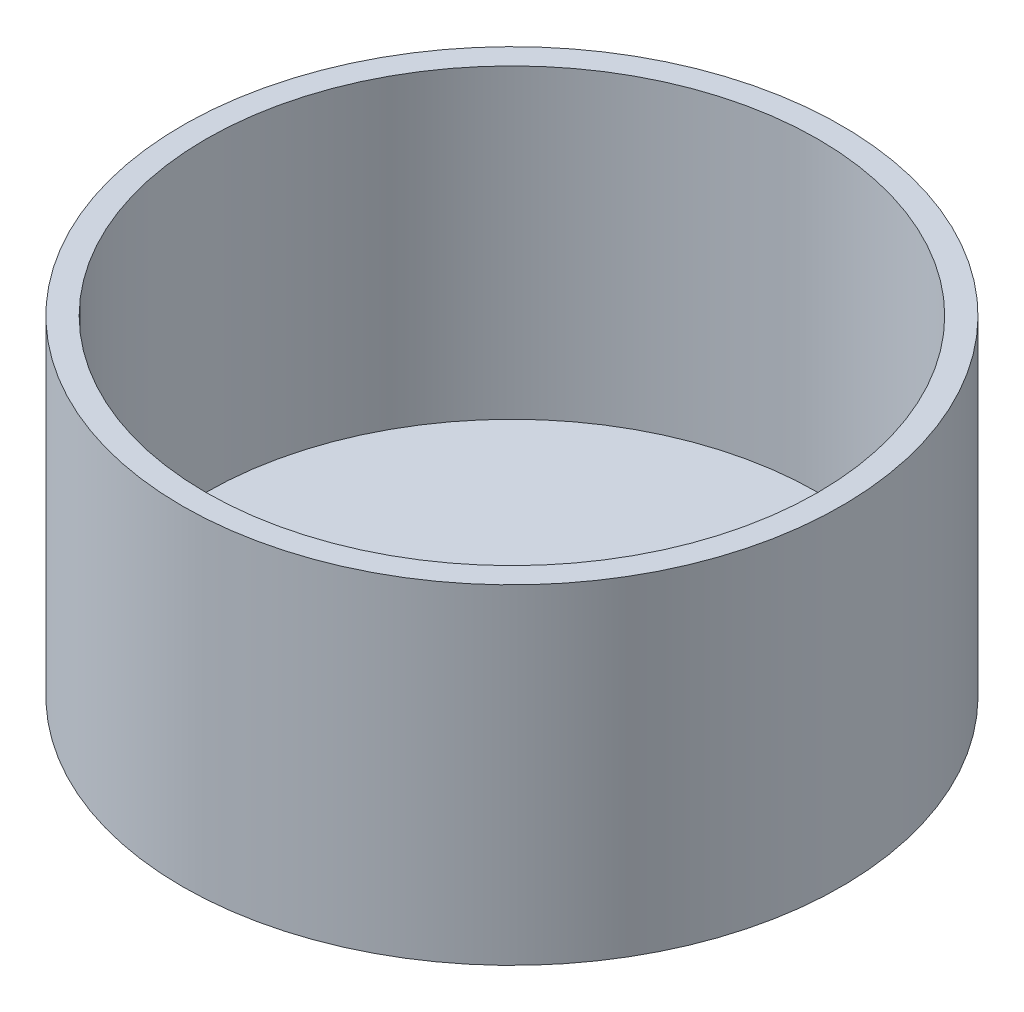
SolidWorks part; units mm, degrees
ref_plane "Спереди" through (0, 0, 0) normal (0, 0, 1) x (1, 0, 0)
ref_plane "Сверху" through (0, 0, 0) normal (0, 1, 0) x (1, 0, 0)
ref_plane "Справа" through (0, 0, 0) normal (1, 0, 0) x (0, 0, -1)
sketch "Sketch1" plane through (0, 0, 0) normal (0, 1, 0) x (1, 0, 0)
  circle A0 centre (0, 0) radius 70
  dimension "D1" = 140
extrude "Boss-Extrude1" add sketch "Sketch1" along normal blind 70
shell "Shell1" thickness 5
